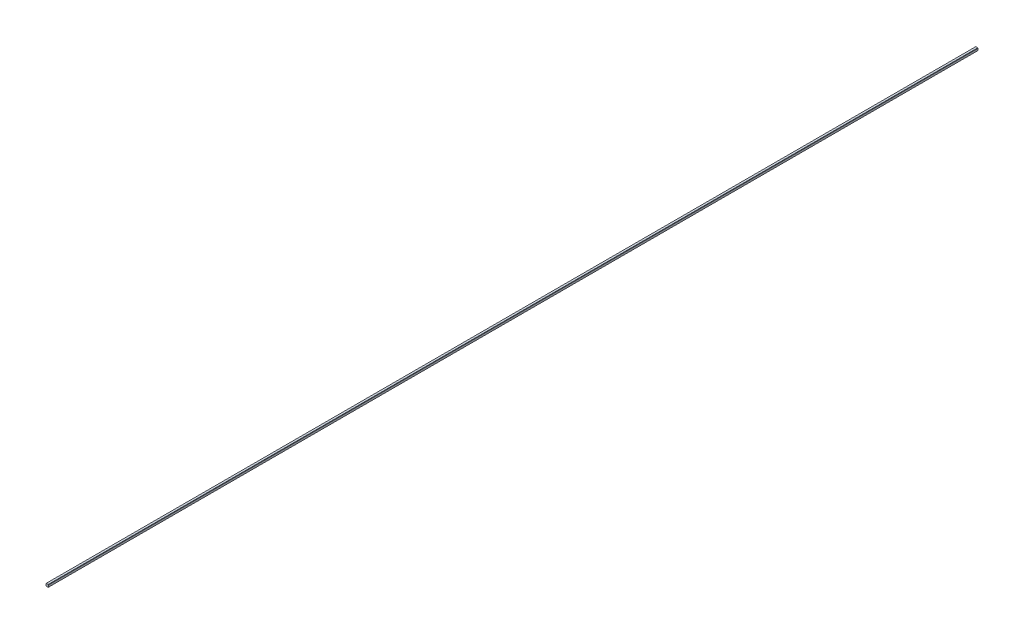
SolidWorks part; units mm, degrees
ref_plane "Front Plane" through (0, 0, 0) normal (0, 0, 1) x (1, 0, 0)
ref_plane "Top Plane" through (0, 0, 0) normal (0, 1, 0) x (1, 0, 0)
ref_plane "Right Plane" through (0, 0, 0) normal (1, 0, 0) x (0, 0, -1)
sketch "Sketch1" plane through (0, 0, 0) normal (0, 0, 1) x (1, 0, 0)
  line L0 (-0.2, 0.25) -> (-0.25, 0.2)
  line L1 (0.2, 0.25) -> (-0.2, 0.25)
  line L2 (0.25, 0.2) -> (0.25, -0.2)
  line L3 (0.2, -0.25) -> (-0.2, -0.25)
  line L4 (-0.25, 0.2) -> (-0.25, -0.2)
  line L5 (0.25, 0.25) -> (-0.25, -0.25) construction
  line L6 (0.25, -0.25) -> (-0.25, 0.25) construction
  line L7 (0.25, 0.2) -> (0.2, 0.25)
  line L8 (0.25, -0.2) -> (0.2, -0.25)
  line L9 (-0.2, -0.25) -> (-0.25, -0.2)
  point P0 (0, 0)
  dimension "D1" = 0.5
  dimension "D2" = 0.5
extrude "Boss-Extrude1" add sketch "Sketch1" along normal blind 185
